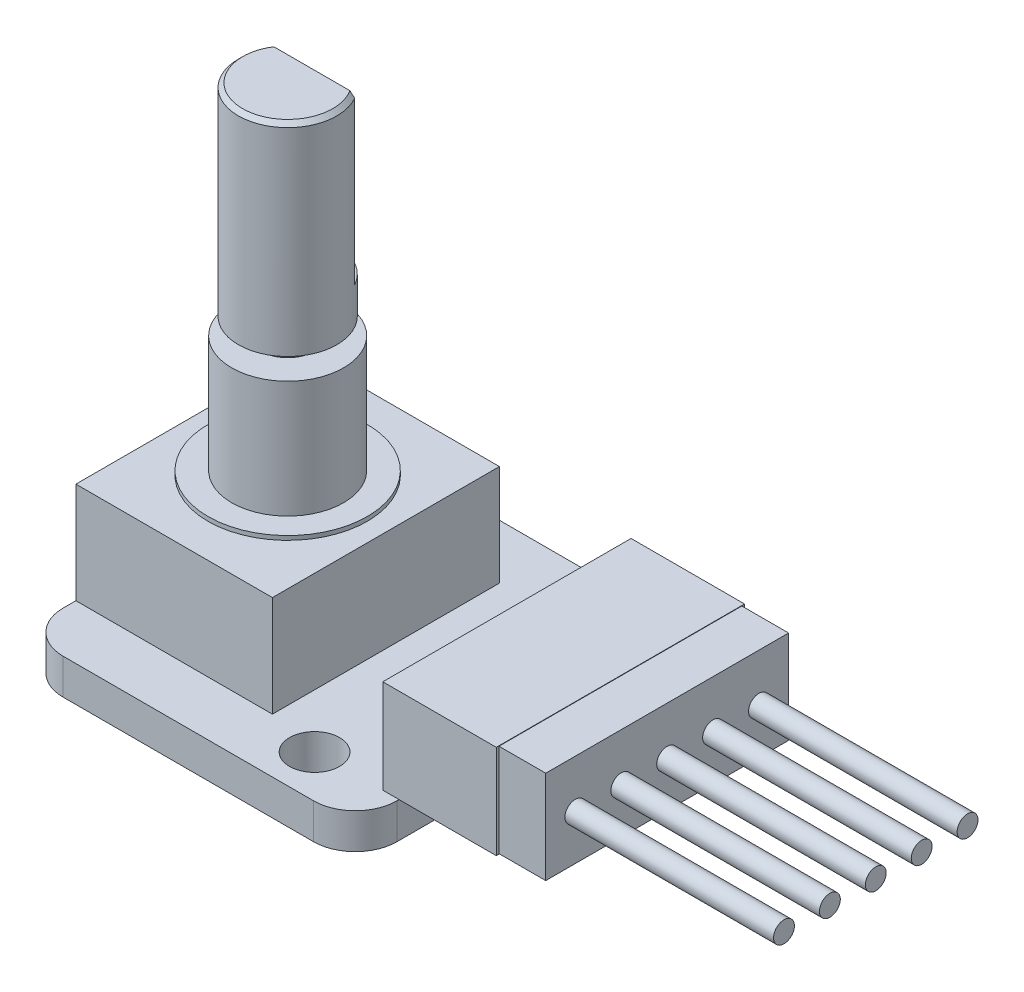
SolidWorks part; units mm, degrees
ref_plane "Front Plane" through (0, 0, 0) normal (0, 0, 1) x (1, 0, 0)
ref_plane "Top Plane" through (0, 0, 0) normal (0, 1, 0) x (1, 0, 0)
ref_plane "Right Plane" through (0, 0, 0) normal (1, 0, 0) x (0, 0, -1)
sketch "Sketch1" plane through (0, 0, 0) normal (0, 1, 0) x (1, 0, 0)
  line L1 (10.16, 10.2235) -> (-10.16, 10.2235)
  line L2 (10.16, 10.2235) -> (10.16, -10.2235)
  line L3 (10.16, -10.2235) -> (-10.16, -10.2235)
  line L4 (-10.16, 10.2235) -> (-10.16, -10.2235)
  line L5 (10.16, 10.2235) -> (-10.16, -10.2235) construction
  line L6 (10.16, -10.2235) -> (-10.16, 10.2235) construction
  point P0 (0, 0)
  dimension "D1" = 20.447
  dimension "D2" = 20.32
extrude "Boss-Extrude1" add sketch "Sketch1" along normal blind 2.159
fillet "Fillet1" radius 2.54 4 edges at (-10.16, 1.0795, -10.2235) (10.16, 1.0795, -10.2235) (10.16, 1.0795, 10.2235) (-10.16, 1.0795, 10.2235)
sketch "Sketch2" plane through (0, 2.159, 0) normal (0, 1, 0) x (1, 0, 0)
  line L0 (10.16, -7.6835) -> (10.16, 7.6835) construction
  line L1 (9.1694, 7.5565) -> (16.0782, 7.5565)
  line L2 (9.1694, 7.5565) -> (9.1694, -7.5565)
  line L3 (9.1694, -7.5565) -> (16.0782, -7.5565)
  line L4 (16.0782, 7.5565) -> (16.0782, -7.5565)
  point P4 (9.1694, 0)
  dimension "D1" = 15.113
  dimension "D2" = 6.9088
  dimension "D3" = 5.9182
extrude "Boss-Extrude2" add sketch "Sketch2" along normal blind 5.715
sketch "Sketch3" plane through (0, 2.159, 0) normal (0, 1, 0) x (1, 0, 0)
  line L0 (-10.16, 7.6835) -> (-10.16, -7.6835) construction
  line L1 (-10.16, 6.9088) -> (1.8034, 6.9088)
  line L2 (-10.16, 6.9088) -> (-10.16, -6.9088)
  line L3 (-10.16, -6.9088) -> (1.8034, -6.9088)
  line L4 (1.8034, 6.9088) -> (1.8034, -6.9088)
  point P6 (1.8034, 0)
  dimension "D1" = 11.9634
  dimension "D2" = 13.8176
extrude "Boss-Extrude3" add sketch "Sketch3" along normal blind 6.1468
sketch "Sketch4" plane through (0, 8.3058, 0) normal (0, 1, 0) x (1, 0, 0)
  line L0 (1.8034, 6.9088) -> (-10.16, 6.9088) construction
  circle A0 centre (-4.1783, 0) radius 4.8514
  point P5 (-4.1783, 6.9088)
  dimension "D1" = 9.7028
extrude "Boss-Extrude4" add sketch "Sketch4" along normal blind 0.254
sketch "Sketch5" plane through (0, 8.5598, 0) normal (0, 1, 0) x (1, 0, 0)
  line L0 (1.8034, 6.9088) -> (-10.16, 6.9088) construction
  circle A0 centre (-4.1783, 0) radius 3.4036
  point P5 (-4.1783, 6.9088)
  dimension "D1" = 6.8072
extrude "Boss-Extrude5" add sketch "Sketch5" along normal blind 7.112
sketch "Sketch6" plane through (0, 15.6718, 0) normal (0, 1, 0) x (1, 0, 0)
  circle A0 centre (-4.1783, 0) radius 1.651
  dimension "D1" = 3.302
extrude "Boss-Extrude6" add sketch "Sketch6" along normal blind 1.016
sketch "Sketch7" plane through (0, 16.6878, 0) normal (0, 1, 0) x (1, 0, 0)
  line L0 (1.8034, 6.9088) -> (-10.16, 6.9088) construction
  circle A0 centre (-4.1783, 0) radius 2.9972
  point P5 (-4.1783, 6.9088)
  dimension "D1" = 5.9944
extrude "Boss-Extrude7" add sketch "Sketch7" along normal blind 12.319
sketch "Sketch8" plane through (0, 29.0068, 0) normal (0, 1, 0) x (1, 0, 0)
  line L0 (-6.7885, 1.4732) -> (-1.5681, 1.4732)
  arc A1 (-6.7885, 1.4732) -> (-1.5681, 1.4732) centre (-4.1783, 0) cw
  dimension "D1" = 2.9972
  dimension "D2" = 1.4732
extrude "Cut-Extrude1" cut sketch "Sketch8" against normal blind 10.0838
sketch "Sketch9" plane through (16.0782, 0, 0) normal (1, 0, 0) x (0, 0, -1)
  line L0 (-7.5565, 7.874) -> (-7.5565, 2.159) construction
  line L1 (7.3914, 7.8486) -> (-7.3914, 7.8486)
  line L2 (7.3914, 7.8486) -> (7.3914, 2.1844)
  line L3 (7.3914, 2.1844) -> (-7.3914, 2.1844)
  line L4 (-7.3914, 7.8486) -> (-7.3914, 2.1844)
  line L5 (7.3914, 7.8486) -> (-7.3914, 2.1844) construction
  line L6 (7.3914, 2.1844) -> (-7.3914, 7.8486) construction
  point P0 (0, 5.0165)
  point P8 (-7.5565, 5.0165)
  dimension "D1" = 14.7828
  dimension "D2" = 5.6642
extrude "Boss-Extrude8" add sketch "Sketch9" along normal blind 2.8448
sketch "Sketch10" plane through (18.923, 0, 0) normal (1, 0, 0) x (0, 0, -1)
  line L0 (-5.588, 4.9358) -> (-2.794, 4.9358) construction
  line L1 (-2.794, 4.9358) -> (0, 4.9358) construction
  line L2 (0, 4.9358) -> (2.794, 4.9358) construction
  line L3 (2.794, 4.9358) -> (5.588, 4.9358) construction
  circle A0 centre (0, 4.9358) radius 0.635
  circle A1 centre (2.794, 4.9358) radius 0.635
  circle A2 centre (5.588, 4.9358) radius 0.635
  circle A3 centre (-2.794, 4.9358) radius 0.635
  circle A4 centre (-5.588, 4.9358) radius 0.635
  dimension "D1" = 1.27
  dimension "D2" = 2.794
extrude "Boss-Extrude9" add sketch "Sketch10" along normal blind 12.7
sketch "Sketch11" plane through (0, 2.159, 0) normal (0, 1, 0) x (1, 0, 0)
  line L1 (5.08, 7.62) -> (5.08, 10.2235) construction
  line L2 (7.62, 10.2235) -> (-7.62, 10.2235) construction
  line L3 (5.08, -7.62) -> (5.08, -10.2235) construction
  line L4 (-7.62, -10.2235) -> (7.62, -10.2235) construction
  circle A0 centre (5.08, 7.62) radius 1.524
  circle A1 centre (5.08, -7.62) radius 1.524
  dimension "D1" = 3.048
  dimension "D2" = 15.24
  dimension "D3" = 5.08
extrude "Cut-Extrude2" cut sketch "Sketch11" against normal blind 12.7
chamfer "Chamfer1" distance 0.254 angle 45 1 edges at (-4.1783, 29.0068, 2.9972)
